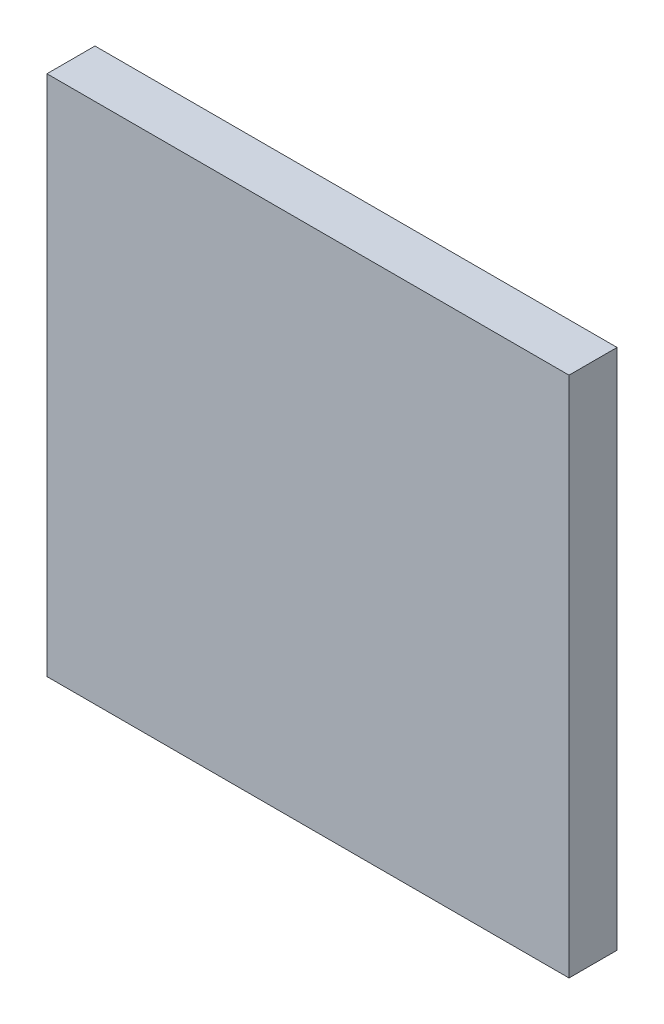
SolidWorks part; units mm, degrees
ref_plane "前视基准面" through (0, 0, 0) normal (0, 0, 1) x (1, 0, 0)
ref_plane "上视基准面" through (0, 0, 0) normal (0, 1, 0) x (1, 0, 0)
ref_plane "右视基准面" through (0, 0, 0) normal (1, 0, 0) x (0, 0, -1)
sketch "草图1" plane through (0, 0, 0) normal (0, 0, 1) x (1, 0, 0)
  line L0 (88.7479, 49.0632) -> (113.7479, 49.0632)
  line L1 (88.7479, 74.0632) -> (113.7479, 74.0632)
  line L2 (88.7479, 74.0632) -> (88.7479, 49.0632)
  line L3 (113.7479, 74.0632) -> (113.7479, 49.0632)
  dimension "D1" = 25
  dimension "D2" = 25
extrude "凸台-拉伸1" add sketch "草图1" along normal blind 2.3
